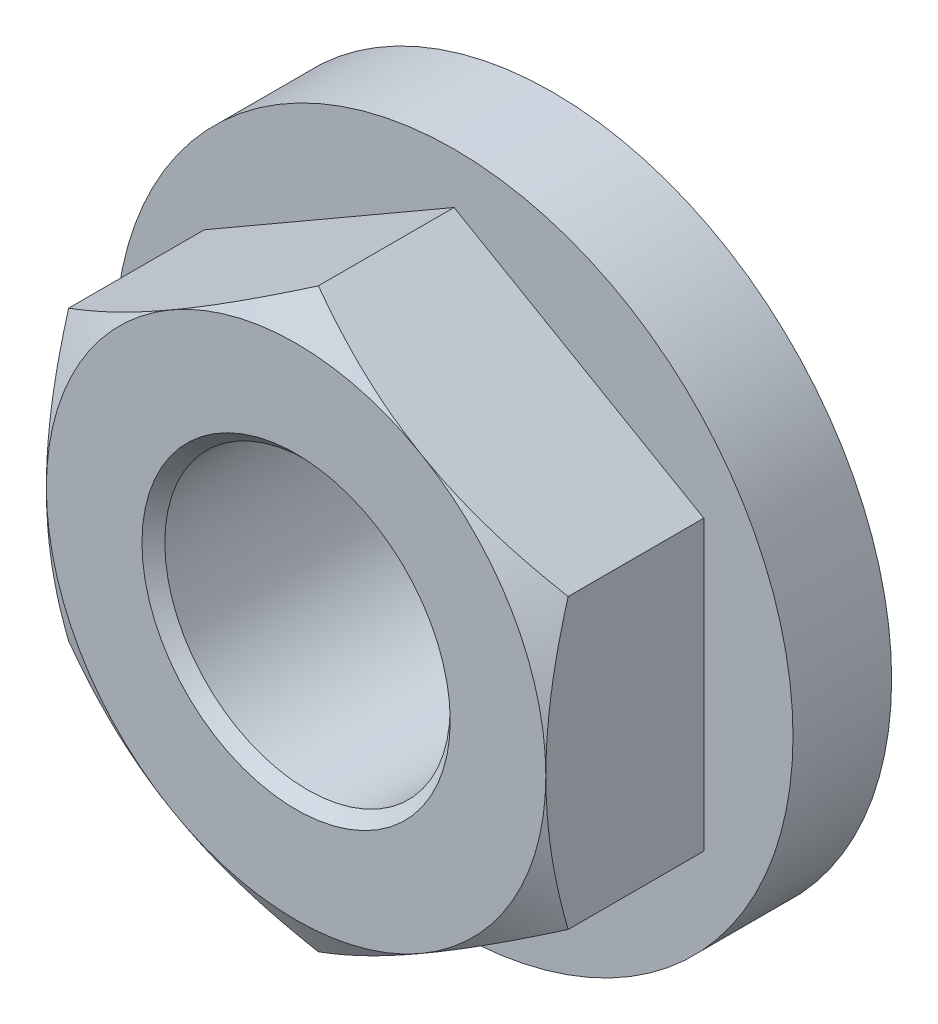
SolidWorks part; units mm, degrees
ref_plane "Front Plane" through (0, 0, 0) normal (0, 0, 1) x (1, 0, 0)
ref_plane "Top Plane" through (0, 0, 0) normal (0, 1, 0) x (1, 0, 0)
ref_plane "Right Plane" through (0, 0, 0) normal (1, 0, 0) x (0, 0, -1)
sketch "Sketch1" plane through (0, 0, 0) normal (0, 0, 1) x (1, 0, 0)
  line L1 (0, 6.4158) -> (-5.5563, 3.2079)
  line L2 (-5.5563, 3.2079) -> (-5.5563, -3.2079)
  line L3 (-5.5563, -3.2079) -> (0, -6.4158)
  line L4 (0, -6.4158) -> (5.5562, -3.2079)
  line L5 (5.5562, -3.2079) -> (5.5562, 3.2079)
  line L6 (5.5562, 3.2079) -> (0, 6.4158)
  circle A0 centre (0, 0) radius 5.5563 construction
  dimension "Hex" = 11.1125
extrude "Extrude1" add sketch "Sketch1" against normal blind 5.9531
sketch "Sketch13" plane through (0, 0, -5.9531) normal (0, 0, -1) x (-1, 0, 0)
  circle A0 centre (0, 0) radius 7.5406
  dimension "Flange od" = 15.0812
extrude "Extrude3" add sketch "Sketch13" against normal blind 2.4384
sketch "Sketch2" plane through (0, 0, 0) normal (0, 0, 1) x (1, 0, 0)
  circle A0 centre (0, 0) radius 5.5563 construction
  circle A1 centre (0, 0) radius 5.5563
extrude "Cut-Extrude1" cut sketch "Sketch2" against normal through all draft 60 flip side to cut
sketch "Sketch4" plane through (0, 0, 0) normal (0, 0, 1) x (1, 0, 0)
  circle A0 centre (0, 0) radius 3.175
  dimension "Thread Dia" = 6.35
extrude "Cut-Extrude3" cut sketch "Sketch4" against normal through all
sketch "Sketch7" plane through (0, 0, 0) normal (0, 0, 1) x (1, 0, 0)
  circle A4 centre (0, 0) radius 3.429
  circle A5 centre (0, 0) radius 3.429
  dimension "D1" = 0.254
sketch "Sketch8" plane through (0, 0, -5.9531) normal (0, 0, -1) x (-1, 0, 0)
  circle A1 centre (0, 0) radius 3.429
  circle A2 centre (0, 0) radius 3.429 construction
sketch "Sketch5" plane through (0, 0, 0) normal (0, 0, 1) x (1, 0, 0)
  circle A0 centre (0, 0) radius 3.175 construction
  circle A1 centre (0, 0) radius 3.175
curve "Helix/Spiral1" pitch 1.27 height 7.2231 turns 5.6875 parameters "pitch"=1.27
sketch "Sketch9" plane through (0, 0, 0) normal (1, 0, 0) x (0, 0, -1)
  line L0 (-0.635, 3.175) -> (-0.4762, 3.175)
  line L1 (-0.4762, 3.175) -> (0, 2.3501)
  line L2 (-0.635, 3.175) -> (-1.1112, 2.3501)
  line L3 (-1.1112, 2.3501) -> (0, 2.3501)
  line L4 (-0.5556, 3.175) -> (-0.5556, 2.3501) construction
  line L5 (-0.8731, 2.7626) -> (-0.2381, 2.7626) construction
  line L7 (0, 2.3501) -> (0, 3.175) construction
  line L8 (0, 3.175) -> (0, -3.175) construction
  dimension "D1" = 0.1588
  dimension "D2" = 0.635
  dimension "D3" = 60
sketch "Sketch12" plane through (0, 0, 0) normal (0, 0, 1) x (1, 0, 0)
  circle A0 centre (0, 0) radius 2.3501
  circle A1 centre (0, 0) radius 3.175 construction
  circle A2 centre (0, 0) radius 3.175
sweep "Cut-Sweep1" cut profiles "Sketch9" path "Helix/Spiral1"
extrude "Cut-Extrude6" cut sketch "Sketch7" against normal through all draft 45
extrude "Cut-Extrude7" cut sketch "Sketch8" against normal through all draft 45
sketch "Sketch14" plane through (0, 0, -5.9531) normal (0, 0, -1) x (-1, 0, 0)
  circle A4 centre (0, 0) radius 5.461
  circle A5 centre (0, 0) radius 5.461
  dimension "D1" = 2.032
extrude "Cut-Extrude8" cut sketch "Sketch14" against normal blind 0.2438 flip side to cut
sketch "Sketch15" plane through (0, 0, -5.7093) normal (0, 0, -1) x (-1, 0, 0)
  line L0 (-0.5353, 5.4347) -> (-0.7391, 7.5043)
  line L1 (0.5353, 5.4347) -> (0.7391, 7.5043)
  line L2 (0, 0) -> (0.5353, 5.4347) construction
  line L3 (0, 0) -> (-0.5353, 5.4347) construction
  circle A0 centre (0, 0) radius 7.5406 construction
  circle A1 centre (0, 0) radius 5.461 construction
  arc A2 (0.7391, 7.5043) -> (-0.7391, 7.5043) centre (0, 0) ccw
  arc A3 (0.5353, 5.4347) -> (-0.5353, 5.4347) centre (0, 0) ccw
  dimension "D1" = 11.25
sketch "Sketch18" plane through (0, 0, -3.5147) normal (0, 0, 1) x (1, 0, 0)
  circle A0 centre (0, 0) radius 7.5406
  circle A1 centre (0, 0) radius 7.5406 construction
equation "\"D2@Sketch9\" = \"pitch@Helix/Spiral1\"*.5"
equation "\"D3@Helix/Spiral1\" = \"pitch@Helix/Spiral1\"+\"Height@Extrude1\""
equation "\"D1@Sketch9\" = \"pitch@Helix/Spiral1\"*.125"
equation "\"D1@Cut-Extrude8\" = \"flange thickness@Extrude3\"*.1"
